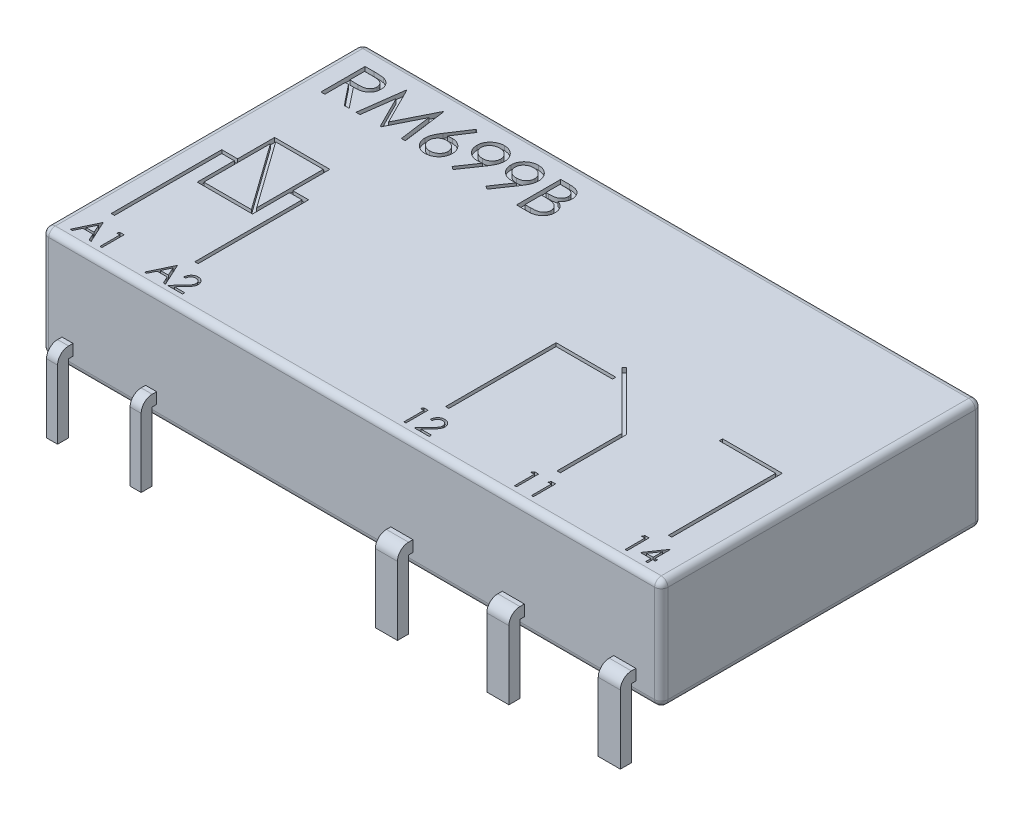
SolidWorks part; units mm, degrees
ref_plane "Front Plane" through (0, 0, 0) normal (0, 0, 1) x (1, 0, 0)
ref_plane "Top Plane" through (0, 0, 0) normal (0, 1, 0) x (1, 0, 0)
ref_plane "Right Plane" through (0, 0, 0) normal (1, 0, 0) x (0, 0, -1)
sketch "Sketch2" plane through (0, 0, 0) normal (0, 1, 0) x (1, 0, 0)
  line L0 (0, 0) -> (0, 0.45) construction
  line L1 (-14, 14.95) -> (14, 14.95)
  line L2 (-14, 14.95) -> (-14, 0.45)
  line L3 (-14, 0.45) -> (14, 0.45)
  line L4 (14, 14.95) -> (14, 0.45)
  dimension "D1" = 0.45
  dimension "D2" = 28
  dimension "D3" = 14.5
extrude "Boss-Extrude1" add sketch "Sketch2" along normal blind 5
ref_plane "Plane1" through (0, 0.6, 0) normal (0, 1, 0) x (1, 0, 0)
sketch "Sketch4" plane through (0, 0.6, 0) normal (0, 1, 0) x (1, 0, 0)
  line L1 (-13.1, 0.25) -> (-12.6, 0.25)
  line L2 (-13.1, 0.25) -> (-13.1, -0.25)
  line L3 (-13.1, -0.25) -> (-12.6, -0.25)
  line L4 (-12.6, 0.25) -> (-12.6, -0.25)
  line L5 (2.27, -0.25) -> (2.27, -1.25) construction
  line L6 (-9.32, 0.25) -> (-8.82, 0.25)
  line L7 (-9.32, 0.25) -> (-9.32, -0.25)
  line L8 (-9.32, -0.25) -> (-8.82, -0.25)
  line L9 (-8.82, 0.25) -> (-8.82, -0.25)
  line L10 (1.77, 0.25) -> (2.77, 0.25)
  line L11 (1.77, 0.25) -> (1.77, -0.25)
  line L12 (1.77, -0.25) -> (2.77, -0.25)
  line L13 (2.77, 0.25) -> (2.77, -0.25)
  line L14 (6.81, 0.25) -> (7.81, 0.25)
  line L15 (6.81, 0.25) -> (6.81, -0.25)
  line L16 (6.81, -0.25) -> (7.81, -0.25)
  line L17 (7.81, 0.25) -> (7.81, -0.25)
  line L18 (11.85, 0.25) -> (12.85, 0.25)
  line L19 (11.85, 0.25) -> (11.85, -0.25)
  line L20 (11.85, -0.25) -> (12.85, -0.25)
  line L21 (12.85, 0.25) -> (12.85, -0.25)
  line L22 (7.31, -0.25) -> (7.31, -1.25) construction
  line L23 (12.35, -0.25) -> (12.35, -1.25) construction
  line L26 (-12.85, -0.25) -> (-12.85, -1.25) construction
  line L27 (-9.07, -0.25) -> (-9.07, -1.25) construction
  line L28 (-14, 0.45) -> (14, 0.45) construction
  line L29 (-14, 14.95) -> (-14, 0.45) construction
  point P4 (1.77, 0)
  dimension "D1" = 0.5
  dimension "D3" = 0.5
  dimension "D4" = 1
  dimension "D5" = 3.78
  dimension "D6" = 5.04
  dimension "D7" = 5.04
  dimension "D8" = 16.38
  dimension "D9" = 0.2
  dimension "D10" = 0.9
  dimension "D11" = 1
extrude "Boss-Extrude2" add sketch "Sketch4" against normal blind 3.1
fillet "Fillet3" radius 0.3 12 edges at (-14, 2.5, -0.45) (-14, 0, -7.7) (-14, 2.5, -14.95) (0, 0, -14.95) (0, 5, -14.95) (0, 5, -0.45) (-14, 5, -7.7) (14, 2.5, -0.45) (14, 5, -7.7) (14, 2.5, -14.95) (14, 0, -7.7) (0, 0, -0.45)
sketch "Sketch6" plane through (0, 5, 0) normal (0, 1, 0) x (1, 0, 0)
  text T0 "A1    A2                         12         11         14" font "Century Gothic" height 1
extrude "Cut-Extrude1" cut sketch "Sketch6" against normal blind 0.2
sketch "Sketch7" plane through (0, 5, 0) normal (0, 1, 0) x (1, 0, 0)
  line L0 (-12.06, 8.836) -> (-9.9093, 5.825)
  line L1 (-12.21, 9.175) -> (-9.71, 9.175)
  line L2 (-12.21, 9.175) -> (-12.21, 7.5)
  line L3 (-12.21, 5.675) -> (-9.71, 5.675)
  line L4 (-9.71, 9.175) -> (-9.71, 7.5)
  line L5 (-12.0107, 9.025) -> (-9.86, 9.025)
  line L6 (-12.06, 8.836) -> (-12.06, 5.825)
  line L7 (-12.06, 5.825) -> (-9.9093, 5.825)
  line L8 (-9.86, 9.025) -> (-9.86, 6.014)
  line L9 (-12.0107, 9.025) -> (-9.86, 6.014)
  line L10 (-12.21, 9.175) -> (-9.71, 5.675) construction
  line L11 (-9.71, 7.35) -> (-9.145, 7.35)
  line L12 (-9.145, 7.35) -> (-9.145, 2.5)
  line L13 (-9.145, 2.5) -> (-8.995, 2.5)
  line L14 (-8.995, 2.5) -> (-8.995, 7.5)
  line L15 (-8.995, 7.5) -> (-9.71, 7.5)
  line L16 (-12.21, 7.5) -> (-12.925, 7.5)
  line L17 (-12.925, 7.5) -> (-12.925, 2.5)
  line L18 (-12.925, 2.5) -> (-12.775, 2.5)
  line L19 (-12.775, 2.5) -> (-12.775, 7.35)
  line L20 (-12.775, 7.35) -> (-12.21, 7.35)
  line L21 (-9.86, 7.425) -> (-8.995, 7.425) construction
  line L22 (-9.07, 0.25) -> (-9.07, 2.5) construction
  line L24 (-12.85, 2.5) -> (-12.85, 0.25) construction
  line L26 (-13.7, 7.7) -> (-12.21, 7.7) construction
  line L27 (-13.7, 14.65) -> (-13.7, 0.75) construction
  line L28 (-12.21, 7.35) -> (-12.21, 5.675)
  line L29 (-9.71, 7.35) -> (-9.71, 5.675)
  line L30 (2.195, 2.5) -> (2.195, 7.5)
  line L31 (2.195, 7.5) -> (4.895, 7.5)
  line L32 (4.895, 7.5) -> (4.895, 7.35)
  line L33 (4.895, 7.35) -> (2.345, 7.35)
  line L34 (2.345, 7.35) -> (2.345, 2.5)
  line L35 (2.345, 2.5) -> (2.195, 2.5)
  line L36 (12.275, 2.5) -> (12.275, 7.35)
  line L37 (12.275, 7.35) -> (9.725, 7.35)
  line L38 (9.725, 7.35) -> (9.725, 7.5)
  line L39 (9.725, 7.5) -> (12.425, 7.5)
  line L40 (12.425, 7.5) -> (12.425, 2.5)
  line L41 (12.425, 2.5) -> (12.275, 2.5)
  line L42 (7.235, 2.5) -> (7.235, 5.4379)
  line L43 (7.235, 5.4379) -> (4.6626, 8.0102)
  line L44 (4.6626, 8.0102) -> (4.7687, 8.1163)
  line L45 (4.7687, 8.1163) -> (7.385, 5.5)
  line L46 (7.385, 5.5) -> (7.385, 2.5)
  line L47 (7.385, 2.5) -> (7.235, 2.5)
  line L48 (2.27, 0.25) -> (2.27, 2.5) construction
  line L50 (12.35, 0.25) -> (12.35, 2.5) construction
  line L52 (7.31, 0.25) -> (7.31, 2.5) construction
  line L54 (2.77, 0.25) -> (1.77, 0.25) construction
  line L55 (7.81, 0.25) -> (6.81, 0.25) construction
  line L56 (12.85, 0.25) -> (11.85, 0.25) construction
  line L57 (-8.82, 0.25) -> (-9.32, 0.25) construction
  line L58 (-12.6, 0.25) -> (-13.1, 0.25) construction
  text T0 "RM699B" font "Century Gothic" height 2
  dimension "D1" = 0.15
  dimension "D2" = 0.15
  dimension "D3" = 0.15
  dimension "D4" = 0.15
  dimension "D5" = 3.5
  dimension "D6" = 2.5
  dimension "D7" = 0.15
  dimension "D8" = 0.15
  dimension "D9" = 0.15
  dimension "D10" = 5
  dimension "D11" = 1.675
  dimension "D12" = 2.5
  dimension "D13" = 0.15
  dimension "D14" = 135
  dimension "D15" = 3
  dimension "D16" = 2.7
  dimension "D17" = 3.7
  dimension "D18" = 12
  dimension "D19" = 13.2
extrude "Cut-Extrude2" cut sketch "Sketch7" against normal blind 0.2
sketch "Sketch8" plane through (0, 0, -0.45) normal (0, 0, 1) x (1, 0, 0)
  line L0 (-12.6, -2.5) -> (-12.6, 0.6) construction
  line L1 (11.85, 0.6) -> (12.85, 0.6)
  line L2 (11.85, 0.6) -> (11.85, 1.1)
  line L3 (11.85, 1.1) -> (12.85, 1.1)
  line L4 (12.85, 0.6) -> (12.85, 1.1)
  line L5 (6.81, 0.6) -> (7.81, 0.6)
  line L6 (6.81, 0.6) -> (6.81, 1.1)
  line L7 (6.81, 1.1) -> (7.81, 1.1)
  line L8 (7.81, 0.6) -> (7.81, 1.1)
  line L9 (1.77, 0.6) -> (2.77, 0.6)
  line L10 (1.77, 0.6) -> (1.77, 1.1)
  line L11 (1.77, 1.1) -> (2.77, 1.1)
  line L12 (2.77, 0.6) -> (2.77, 1.1)
  line L13 (-9.32, 0.6) -> (-8.82, 0.6)
  line L14 (-9.32, 0.6) -> (-9.32, 1.1)
  line L15 (-9.32, 1.1) -> (-8.82, 1.1)
  line L16 (-8.82, 0.6) -> (-8.82, 1.1)
  line L17 (-13.1, 0.6) -> (-12.6, 0.6)
  line L18 (-13.1, 0.6) -> (-13.1, 1.1)
  line L19 (-13.1, 1.1) -> (-12.6, 1.1)
  line L20 (-12.6, 0.6) -> (-12.6, 1.1)
  line L21 (-8.82, -2.5) -> (-8.82, 0.6) construction
  line L22 (2.77, -2.5) -> (2.77, 0.6) construction
  line L23 (7.81, -2.5) -> (7.81, 0.6) construction
  line L24 (12.85, -2.5) -> (12.85, 0.6) construction
extrude "Boss-Extrude3" add sketch "Sketch8" along normal up to vertex (0.7 mm away)
fillet "Fillet4" radius 0.5 5 edges at (12.35, 1.1, 0.25) (7.31, 1.1, 0.25) (2.27, 1.1, 0.25) (-9.07, 1.1, 0.25) (-12.85, 1.1, 0.25)
